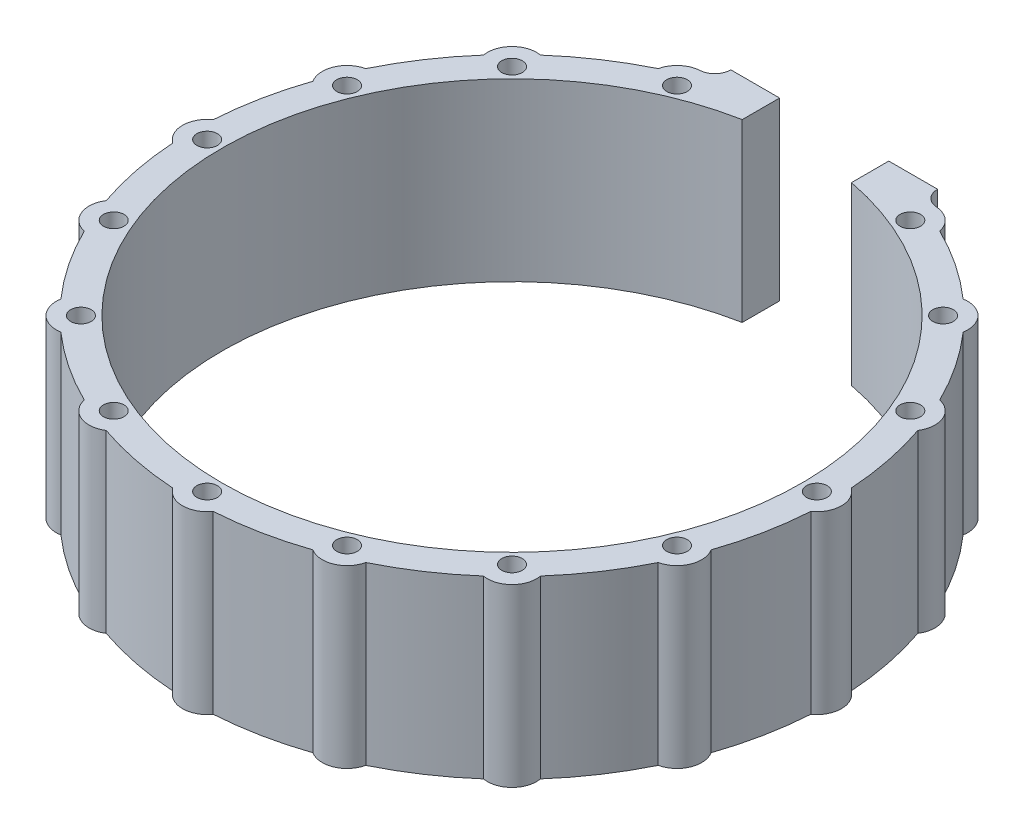
SolidWorks part; units mm, degrees
ref_plane "Front Plane" through (0, 0, 0) normal (0, 0, 1) x (1, 0, 0)
ref_plane "Top Plane" through (0, 0, 0) normal (0, 1, 0) x (1, 0, 0)
ref_plane "Right Plane" through (0, 0, 0) normal (1, 0, 0) x (0, 0, -1)
sketch "Sketch1" plane through (0, 0, 0) normal (0, 1, 0) x (1, 0, 0)
  line L15 (-8.7768, 45.7902) -> (-8.7768, 51.7982)
  line L16 (-8.7768, 51.7982) -> (-16.6231, 51.7982)
  line L17 (-16.6231, 51.7982) -> (-16.6231, 51.7706)
  line L18 (16.6231, 51.7706) -> (16.6231, 51.7982)
  line L20 (16.6231, 51.7982) -> (8.7768, 51.7982)
  line L22 (8.7768, 51.7982) -> (8.7768, 45.7902)
  line L24 (-8.7768, 45.7902) -> (-8.7768, 51.7982)
  line L25 (-8.7768, 51.7982) -> (-16.6231, 51.7982)
  line L26 (-16.6231, 51.7982) -> (-16.6231, 51.7706)
  line L28 (16.6231, 51.7706) -> (16.6231, 51.7982)
  line L29 (16.6231, 51.7982) -> (8.7768, 51.7982)
  line L30 (8.7768, 51.7982) -> (8.7768, 45.7902)
  circle A23 centre (-18.7534, 45.2747) radius 1.651 construction
  circle A25 centre (-34.6518, 34.6518) radius 1.651 construction
  circle A27 centre (-45.2747, 18.7534) radius 1.651 construction
  circle A29 centre (-49.005, 0) radius 1.651 construction
  circle A32 centre (-45.2747, -18.7534) radius 1.651 construction
  circle A34 centre (-34.6518, -34.6518) radius 1.651 construction
  circle A36 centre (-18.7534, -45.2747) radius 1.651 construction
  circle A38 centre (0, -49.005) radius 1.651 construction
  circle A40 centre (18.7534, -45.2747) radius 1.651 construction
  circle A42 centre (18.7534, 45.2747) radius 1.651 construction
  circle A87 centre (34.6518, 34.6518) radius 1.651 construction
  circle A88 centre (45.2747, 18.7534) radius 1.651 construction
  circle A89 centre (49.005, 0) radius 1.651 construction
  circle A90 centre (45.2747, -18.7534) radius 1.651 construction
  circle A91 centre (34.6518, -34.6518) radius 1.651 construction
  circle A92 centre (18.7534, 45.2747) radius 1.651
  circle A93 centre (34.6518, 34.6518) radius 1.651
  circle A94 centre (45.2747, 18.7534) radius 1.651
  circle A95 centre (49.005, 0) radius 1.651
  circle A96 centre (45.2747, -18.7534) radius 1.651
  circle A97 centre (34.6518, -34.6518) radius 1.651
  circle A98 centre (18.7534, -45.2747) radius 1.651
  circle A100 centre (0, -49.005) radius 1.651
  circle A102 centre (-18.7534, -45.2747) radius 1.651
  circle A104 centre (-34.6518, -34.6518) radius 1.651
  circle A106 centre (-45.2747, -18.7534) radius 1.651
  circle A107 centre (-49.005, 0) radius 1.651
  circle A108 centre (-45.2747, 18.7534) radius 1.651
  circle A109 centre (-34.6518, 34.6518) radius 1.651
  circle A110 centre (-18.7534, 45.2747) radius 1.651
  arc A113 (-19.0032, 49.2356) -> (-16.6231, 51.7706) centre (-19.1631, 51.7706) ccw
  arc A114 (-19.0032, 49.2356) -> (-22.6275, 46.1361) centre (-18.7534, 45.2747) ccw
  arc A115 (-22.6275, 46.1361) -> (-33.965, 38.5607) centre (0, 0) ccw
  arc A116 (-33.965, 38.5607) -> (-38.5607, 33.965) centre (-34.6518, 34.6518) ccw
  arc A117 (-38.5607, 33.965) -> (-46.1361, 22.6275) centre (0, 0) ccw
  arc A118 (-46.1361, 22.6275) -> (-48.6232, 16.6231) centre (-45.2747, 18.7534) ccw
  arc A119 (-48.6232, 16.6231) -> (-51.2834, 3.2496) centre (0, 0) ccw
  arc A120 (-51.2834, 3.2496) -> (-51.2834, -3.2496) centre (-49.005, 0) ccw
  arc A121 (-51.2834, -3.2496) -> (-48.6232, -16.6231) centre (0, 0) ccw
  arc A122 (-48.6232, -16.6231) -> (-46.1361, -22.6275) centre (-45.2747, -18.7534) ccw
  arc A123 (-46.1361, -22.6275) -> (-38.5607, -33.965) centre (0, 0) ccw
  arc A124 (-38.5607, -33.965) -> (-33.965, -38.5607) centre (-34.6518, -34.6518) ccw
  arc A125 (-33.965, -38.5607) -> (-22.6275, -46.1361) centre (0, 0) ccw
  arc A126 (-22.6275, -46.1361) -> (-16.6231, -48.6232) centre (-18.7534, -45.2747) ccw
  arc A127 (-16.6231, -48.6232) -> (-3.2496, -51.2834) centre (0, 0) ccw
  arc A128 (-3.2496, -51.2834) -> (3.2496, -51.2834) centre (0, -49.005) ccw
  arc A130 (3.2496, -51.2834) -> (16.6231, -48.6232) centre (0, 0) ccw
  arc A132 (16.6231, -48.6232) -> (22.6275, -46.1361) centre (18.7534, -45.2747) ccw
  arc A134 (22.6275, -46.1361) -> (33.965, -38.5607) centre (0, 0) ccw
  arc A136 (33.965, -38.5607) -> (38.5607, -33.965) centre (34.6518, -34.6518) ccw
  arc A138 (38.5607, -33.965) -> (46.1361, -22.6275) centre (0, 0) ccw
  arc A140 (46.1361, -22.6275) -> (48.6232, -16.6231) centre (45.2747, -18.7534) ccw
  arc A142 (48.6232, -16.6231) -> (51.2834, -3.2496) centre (0, 0) ccw
  arc A144 (51.2834, -3.2496) -> (51.2834, 3.2496) centre (49.005, 0) ccw
  arc A177 (51.2834, 3.2496) -> (48.6232, 16.6231) centre (0, 0) ccw
  arc A179 (48.6232, 16.6231) -> (46.1361, 22.6275) centre (45.2747, 18.7534) ccw
  arc A180 (46.1361, 22.6275) -> (38.5607, 33.965) centre (0, 0) ccw
  arc A181 (38.5607, 33.965) -> (33.965, 38.5607) centre (34.6518, 34.6518) ccw
  arc A182 (33.965, 38.5607) -> (22.6275, 46.1361) centre (0, 0) ccw
  arc A183 (22.6275, 46.1361) -> (19.0032, 49.2356) centre (18.7534, 45.2747) ccw
  arc A184 (16.6231, 51.7706) -> (19.0032, 49.2356) centre (19.1631, 51.7706) ccw
  arc A185 (-8.7768, 45.7902) -> (8.7768, 45.7902) centre (0, 0) ccw
  arc A186 (-19.0032, 49.2356) -> (-16.6231, 51.7706) centre (-19.1631, 51.7706) ccw
  arc A187 (-19.0032, 49.2356) -> (-22.6275, 46.1361) centre (-18.7534, 45.2747) ccw
  arc A188 (-22.6275, 46.1361) -> (-33.965, 38.5607) centre (0, 0) ccw
  arc A189 (-33.965, 38.5607) -> (-38.5607, 33.965) centre (-34.6518, 34.6518) ccw
  arc A190 (-38.5607, 33.965) -> (-46.1361, 22.6275) centre (0, 0) ccw
  arc A191 (-46.1361, 22.6275) -> (-48.6232, 16.6231) centre (-45.2747, 18.7534) ccw
  arc A192 (-48.6232, 16.6231) -> (-51.2834, 3.2496) centre (0, 0) ccw
  arc A193 (-51.2834, 3.2496) -> (-51.2834, -3.2496) centre (-49.005, 0) ccw
  arc A194 (-51.2834, -3.2496) -> (-48.6232, -16.6231) centre (0, 0) ccw
  arc A195 (-48.6232, -16.6231) -> (-46.1361, -22.6275) centre (-45.2747, -18.7534) ccw
  arc A196 (-46.1361, -22.6275) -> (-38.5607, -33.965) centre (0, 0) ccw
  arc A197 (-38.5607, -33.965) -> (-33.965, -38.5607) centre (-34.6518, -34.6518) ccw
  arc A198 (-33.965, -38.5607) -> (-22.6275, -46.1361) centre (0, 0) ccw
  arc A199 (-22.6275, -46.1361) -> (-16.6231, -48.6232) centre (-18.7534, -45.2747) ccw
  arc A200 (-16.6231, -48.6232) -> (-3.2496, -51.2834) centre (0, 0) ccw
  arc A202 (-3.2496, -51.2834) -> (3.2496, -51.2834) centre (0, -49.005) ccw
  arc A204 (3.2496, -51.2834) -> (16.6231, -48.6232) centre (0, 0) ccw
  arc A205 (16.6231, -48.6232) -> (22.6275, -46.1361) centre (18.7534, -45.2747) ccw
  arc A206 (22.6275, -46.1361) -> (33.965, -38.5607) centre (0, 0) ccw
  arc A207 (33.965, -38.5607) -> (38.5607, -33.965) centre (34.6518, -34.6518) ccw
  arc A208 (38.5607, -33.965) -> (46.1361, -22.6275) centre (0, 0) ccw
  arc A209 (46.1361, -22.6275) -> (48.6232, -16.6231) centre (45.2747, -18.7534) ccw
  arc A210 (48.6232, -16.6231) -> (51.2834, -3.2496) centre (0, 0) ccw
  arc A211 (51.2834, -3.2496) -> (51.2834, 3.2496) centre (49.005, 0) ccw
  arc A212 (51.2834, 3.2496) -> (48.6232, 16.6231) centre (0, 0) ccw
  arc A213 (48.6232, 16.6231) -> (46.1361, 22.6275) centre (45.2747, 18.7534) ccw
  arc A214 (46.1361, 22.6275) -> (38.5607, 33.965) centre (0, 0) ccw
  arc A215 (38.5607, 33.965) -> (33.965, 38.5607) centre (34.6518, 34.6518) ccw
  arc A216 (33.965, 38.5607) -> (22.6275, 46.1361) centre (0, 0) ccw
  arc A217 (22.6275, 46.1361) -> (19.0032, 49.2356) centre (18.7534, 45.2747) ccw
  arc A218 (16.6231, 51.7706) -> (19.0032, 49.2356) centre (19.1631, 51.7706) ccw
  arc A219 (-8.7768, 45.7902) -> (8.7768, 45.7902) centre (0, 0) ccw
  dimension "D1" = 0
extrude "Boss-Extrude1" add sketch "Sketch1" along normal up to surface (28.25 mm away) from surface at -14.125
